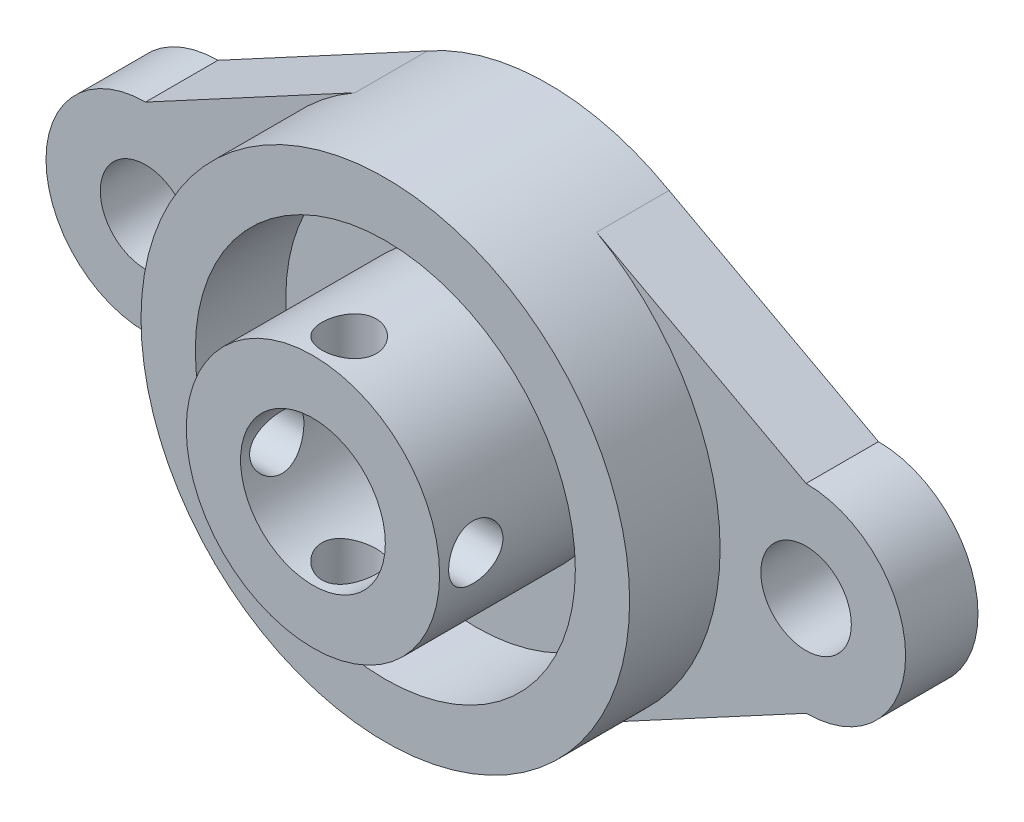
SolidWorks part; units mm, degrees
ref_plane "Plano frontal" through (0, 0, 0) normal (0, 0, 1) x (1, 0, 0)
ref_plane "Plano superior" through (0, 0, 0) normal (0, 1, 0) x (1, 0, 0)
ref_plane "Plano direito" through (0, 0, 0) normal (1, 0, 0) x (0, 0, -1)
sketch "Esboço1" plane through (0, 0, 0) normal (0, 0, 1) x (1, 0, 0)
  line L0 (-18.25, 5.5) -> (-6.6777, 11.7328)
  line L2 (6.6777, 11.7328) -> (18.25, 5.5)
  line L3 (-18.25, -5.5) -> (-6.6777, -11.7328)
  line L5 (6.6777, -11.7328) -> (18.25, -5.5)
  arc A0 (-6.6777, -11.7328) -> (6.6777, -11.7328) centre (0, 0) ccw
  circle A1 centre (-18.25, 0) radius 2.5
  circle A2 centre (18.25, 0) radius 2.5
  arc A3 (-18.25, 5.5) -> (-18.25, -5.5) centre (-18.25, 0) ccw
  arc A4 (18.25, -5.5) -> (18.25, 5.5) centre (18.25, 0) ccw
  arc A5 (6.6777, 11.7328) -> (-6.6777, 11.7328) centre (0, 0) ccw
  circle A6 centre (0, 0) radius 4
  dimension "D1" = 5
  dimension "D2" = 5
  dimension "D3" = 11
  dimension "D4" = 11
  dimension "D5" = 27
  dimension "D6" = 36.5
  dimension "D7" = 18.25
  dimension "D8" = 8
extrude "Ressalto-extrusão1" add sketch "Esboço1" along normal blind 4
sketch "Esboço2" plane through (0, 0, 4) normal (0, 0, 1) x (1, 0, 0)
  circle A0 centre (0, 0) radius 13.5
  circle A1 centre (0, 0) radius 10.5
  dimension "D1" = 21
extrude "Ressalto-extrusão2" add sketch "Esboço2" along normal blind 5
sketch "Esboço3" plane through (0, 0, 4) normal (0, 0, 1) x (1, 0, 0)
  circle A0 centre (0, 0) radius 4
  circle A1 centre (0, 0) radius 7
  dimension "D1" = 14
extrude "Ressalto-extrusão3" add sketch "Esboço3" along normal blind 9
sketch "Esboço4" plane through (0, 0, 0) normal (0, 1, 0) x (1, 0, 0)
  line L0 (-7, -13) -> (7, -13) construction
  circle A0 centre (0, -11) radius 1.5
  dimension "D1" = 3
  dimension "D2" = 2
extrude "Corte-extrusão1" cut sketch "Esboço4" against normal through all both and the other way through all
sketch "Esboço5" plane through (0, 0, 0) normal (1, 0, 0) x (0, 0, -1)
  line L0 (-13, 7) -> (-13, -7) construction
  circle A0 centre (-11, 0) radius 1.5
  dimension "D1" = 3
  dimension "D2" = 2
extrude "Corte-extrusão2" cut sketch "Esboço5" against normal through all both and the other way through all
